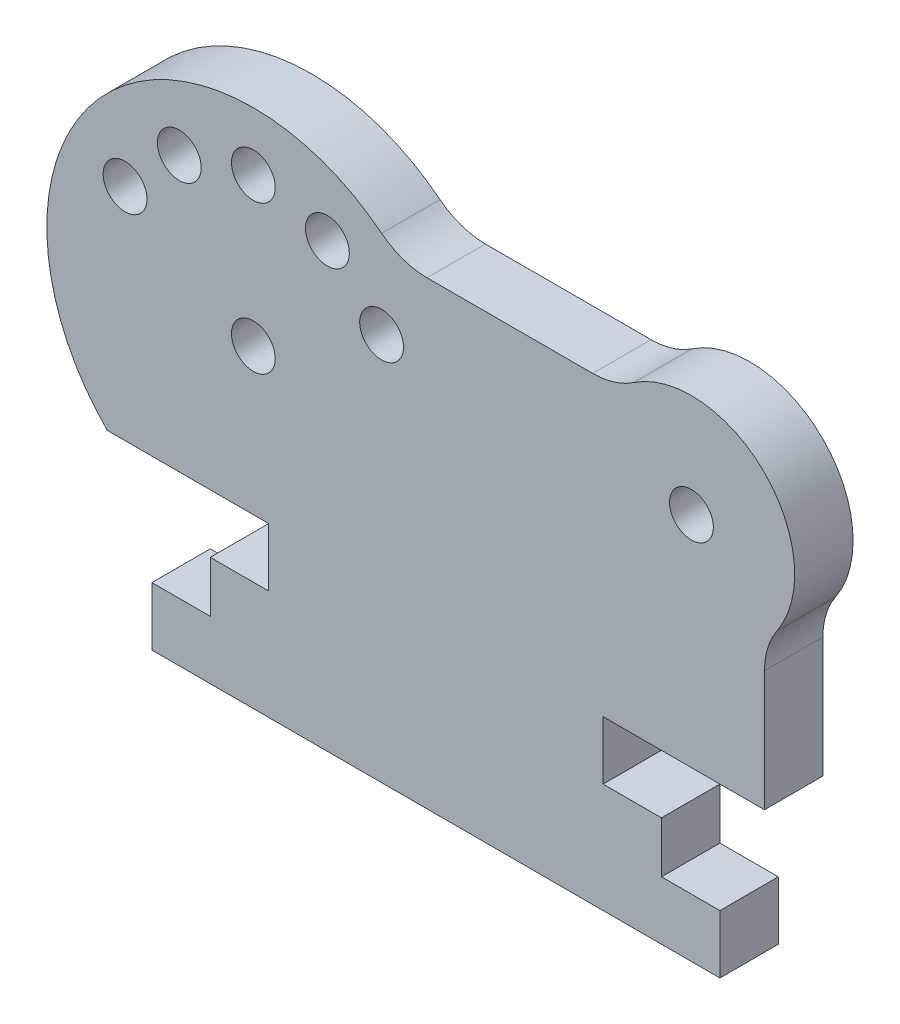
SolidWorks part; units mm, degrees
ref_plane "Front Plane" through (0, 0, 0) normal (0, 0, 1) x (1, 0, 0)
ref_plane "Top Plane" through (0, 0, 0) normal (0, 1, 0) x (1, 0, 0)
ref_plane "Right Plane" through (0, 0, 0) normal (1, 0, 0) x (0, 0, -1)
sketch "Sketch2" plane through (0, 0, 0) normal (0, 0, 1) x (1, 0, 0)
  line L0 (0, 0) -> (0, 4)
  line L1 (0, 4) -> (4, 4)
  line L2 (4, 4) -> (4, 7.5)
  line L3 (4, 7.5) -> (8, 7.5)
  line L4 (8, 7.5) -> (8, 11.5)
  line L5 (8, 11.5) -> (-3.05, 11.5)
  line L6 (-3.05, 31.5) -> (41.95, 31.5)
  line L7 (41.95, 31.5) -> (41.95, 11.5)
  line L8 (41.95, 11.5) -> (30.9, 11.5)
  line L9 (30.9, 11.5) -> (30.9, 7.5)
  line L10 (30.9, 7.5) -> (34.9, 7.5)
  line L11 (34.9, 7.5) -> (34.9, 4)
  line L12 (34.9, 4) -> (38.9, 4)
  line L13 (38.9, 4) -> (38.9, 0)
  line L14 (38.9, 0) -> (0, 0)
  line L15 (-3.05, 31.5) -> (-3.05, 11.5)
  line L16 (6.95, 21.5) -> (15.7333, 26.5711) construction
  line L17 (0.74, 27.71) -> (23.16, 27.71)
  line L18 (0.74, 27.71) -> (0.74, 15.29)
  line L19 (0.74, 15.29) -> (23.16, 15.29)
  line L20 (23.16, 27.71) -> (23.16, 15.29)
  line L21 (6.95, 21.5) -> (6.95, 31.6421) construction
  circle A1 centre (6.95, 21.5) radius 14.1421
  circle A2 centre (36.95, 26.5) radius 1.5
  circle A4 centre (36.95, 26.5) radius 7.0711
  circle A5 centre (6.95, 21.5) radius 6.21
  circle A6 centre (6.95, 21.5) radius 1.5
  circle A7 centre (6.95, 21.5) radius 10.1421 construction
  circle A8 centre (15.7333, 26.5711) radius 1.5
  circle A9 centre (6.95, 21.5) radius 10.1421 construction
  circle A10 centre (12.0211, 30.2833) radius 1.5
  circle A11 centre (6.95, 21.5) radius 10.1421 construction
  circle A12 centre (6.95, 31.6421) radius 1.5
  circle A13 centre (6.95, 21.5) radius 10.1421 construction
  circle A14 centre (1.8789, 30.2833) radius 1.5
  circle A15 centre (6.95, 21.5) radius 10.1421 construction
  circle A16 centre (-1.8333, 26.5711) radius 1.5
  point P2 (0.74, 21.5)
  point P3 (19.45, 0)
  point P10 (19.45, 31.5)
  point P24 (-3.05, 21.5)
  point P37 (0, 0)
  point P51 (6.95, 21.5)
  dimension "D5" = 22.42
  dimension "D10" = 30
  dimension "D13" = 3
  dimension "D15" = 3
  dimension "D7" = 10
  dimension "D9" = 4
  dimension "D17" = 3
  dimension "D1" = 4
  dimension "D2" = 22.9
  dimension "D3" = 4
  dimension "D4" = 4
  dimension "D6" = 12.42
  dimension "D8" = 10
  dimension "D11" = 5
  dimension "D12" = 5
  dimension "D14" = 3.5
  dimension "D16" = 60
  dimension "D18" = 5
extrude "Boss-Extrude1" add sketch "Sketch2" along normal blind 4 contours L15 A1 | L17 A1 L6 L15 L5 L4 L19 L18 | L6 A1 | L6 A4 L7 A2 | L6 A4 | L7 A4 | A4 L6 A1 L17 L20 L19 L4 L3 L2 L1 L0 L14 L13 L12 L11 L10 L9 L8 L7 | A5 L18 L19 | A5 L17 L18 | A5 L19 A1 L17 | A1 L19 L20 L17 | A6
fillet "Fillet1" radius 5 3 edges at (41.95, 21.5, 2) (31.95, 31.5, 2) (16.95, 31.5, 2)
